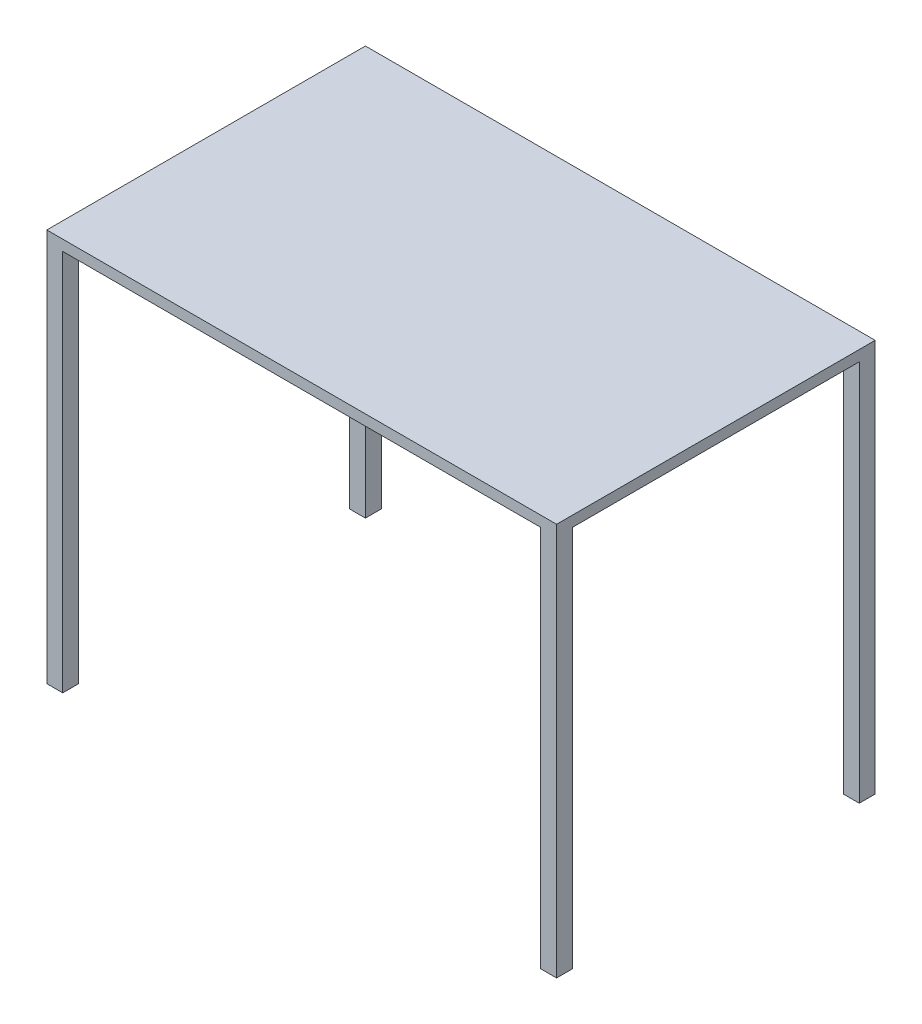
SolidWorks part; units mm, degrees
ref_plane "Front Plane" through (0, 0, 0) normal (0, 0, 1) x (1, 0, 0)
ref_plane "Top Plane" through (0, 0, 0) normal (0, 1, 0) x (1, 0, 0)
ref_plane "Right Plane" through (0, 0, 0) normal (1, 0, 0) x (0, 0, -1)
sketch "Sketch1" plane through (0, 0, 0) normal (0, 1, 0) x (1, 0, 0)
  line L1 (-609.6, -381) -> (609.6, -381)
  line L2 (-609.6, -381) -> (-609.6, 381)
  line L3 (-609.6, 381) -> (609.6, 381)
  line L4 (609.6, -381) -> (609.6, 381)
  line L5 (-609.6, -381) -> (609.6, 381) construction
  line L6 (-609.6, 381) -> (609.6, -381) construction
  point P0 (0, 0)
  dimension "D1" = 762
  dimension "D2" = 1219.2
extrude "Boss-Extrude1" add sketch "Sketch1" along normal blind 25.4
sketch "Sketch3" plane through (0, 0, 0) normal (0, -1, 0) x (1, 0, 0)
  line L0 (0, 381) -> (0, -374.1471) construction
  line L1 (-609.6, 381) -> (-571.5, 381)
  line L2 (-609.6, 381) -> (-609.6, 342.9)
  line L3 (-609.6, 342.9) -> (-571.5, 342.9)
  line L4 (-571.5, 381) -> (-571.5, 342.9)
  line L5 (-609.6, 381) -> (609.6, 381) construction
  line L6 (0, -374.1471) -> (609.6, 0) construction
  line L7 (609.6, 381) -> (609.6, -381) construction
  line L8 (609.6, 0) -> (-609.6, 0) construction
  line L9 (-609.6, -381) -> (-609.6, 381) construction
  line L10 (571.5, 381) -> (571.5, 342.9)
  line L11 (609.6, 342.9) -> (571.5, 342.9)
  line L12 (609.6, 381) -> (609.6, 342.9)
  line L13 (609.6, 381) -> (571.5, 381)
  line L14 (609.6, -381) -> (571.5, -381)
  line L15 (609.6, -381) -> (609.6, -342.9)
  line L16 (609.6, -342.9) -> (571.5, -342.9)
  line L17 (571.5, -381) -> (571.5, -342.9)
  line L18 (-571.5, -381) -> (-571.5, -342.9)
  line L19 (-609.6, -342.9) -> (-571.5, -342.9)
  line L20 (-609.6, -381) -> (-609.6, -342.9)
  line L21 (-609.6, -381) -> (-571.5, -381)
  dimension "D1" = 38.1
  dimension "D2" = 38.1
extrude "Boss-Extrude2" add sketch "Sketch3" along normal blind 914.4
